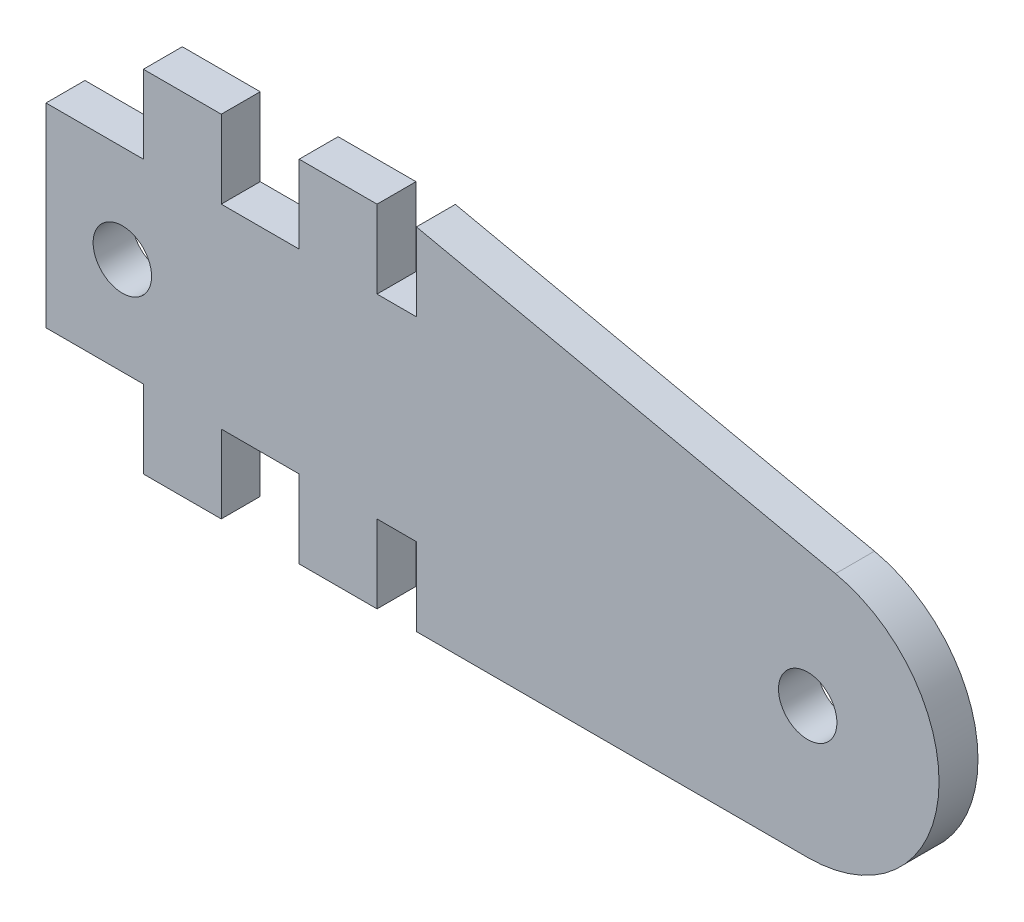
SolidWorks part; units mm, degrees
ref_plane "Front Plane" through (0, 0, 0) normal (0, 0, 1) x (1, 0, 0)
ref_plane "Top Plane" through (0, 0, 0) normal (0, 1, 0) x (1, 0, 0)
ref_plane "Right Plane" through (0, 0, 0) normal (1, 0, 0) x (0, 0, -1)
sketch "Sketch1" plane through (0, 0, 0) normal (0, 0, 1) x (1, 0, 0)
  line L0 (5, 0) -> (9, 0)
  line L1 (5, 4) -> (5, 0)
  line L2 (5, 14) -> (0, 14)
  line L3 (9, 4) -> (13, 4)
  line L4 (13, 4) -> (13, 0)
  line L5 (9, 0) -> (9, 4)
  line L6 (13, 0) -> (17, 0)
  line L7 (17, 0) -> (17, 4)
  line L8 (17, 4) -> (19.0216, 4)
  line L9 (0, 14) -> (0, 4)
  line L10 (19.0216, 4) -> (19.0216, 0)
  line L11 (17, 14) -> (19.0216, 14)
  line L12 (17, 18) -> (17, 14)
  line L13 (13, 18) -> (17, 18)
  line L14 (9, 18) -> (9, 14)
  line L15 (13, 14) -> (13, 18)
  line L16 (9, 14) -> (13, 14)
  line L17 (0, 4) -> (5, 4)
  line L18 (5, 14) -> (5, 18)
  line L19 (5, 18) -> (9, 18)
  line L20 (19.0216, 0) -> (39.1145, 0)
  line L21 (29.045, 0) -> (29.045, -6.4753) construction
  line L22 (19.0216, 14) -> (19.0216, 18)
  line L23 (19.0216, 18) -> (40.5426, 13.3378)
  line L27 (23.6391, 12.0249) -> (21.6695, 11.6776) construction
  line L32 (16.7455, 10.8093) -> (17.6137, 5.8853) construction
  line L33 (16.7455, 10.8093) -> (14.7759, 10.462) construction
  line L34 (14.7759, 10.462) -> (15.6441, 5.538) construction
  line L35 (15.6441, 5.538) -> (17.6137, 5.8853) construction
  line L36 (21.6695, 11.6776) -> (22.5378, 6.7535) construction
  line L37 (22.5378, 6.7535) -> (24.5074, 7.1008) construction
  line L38 (23.6391, 12.0249) -> (24.5074, 7.1008) construction
  arc A0 (39.1145, 0) -> (40.5426, 13.3378) centre (39.1145, 6.7453) ccw
  circle A1 centre (3.9205, 9) radius 1.5
  circle A2 centre (39.1145, 6.7453) radius 12.12 construction
  circle A4 centre (39.1145, 6.7453) radius 1.5
  dimension "D16" = 9
  dimension "D13" = 5.8853
  dimension "D1" = 3
  dimension "D2" = 6.7453
  dimension "D7" = 24.24
  dimension "D3" = 3.9205
  dimension "D4" = 14.7759
  dimension "D5" = 15.6441
  dimension "D6" = 16.7455
  dimension "D8" = 21.6695
  dimension "D9" = 9
  dimension "D10" = 18
  dimension "D11" = 19.0216
  dimension "D12" = 5.538
  dimension "ThumbLinkLengthMCP" = 20.045
extrude "Boss-Extrude1" add sketch "Sketch1" along normal blind 2
equation "\"ThumbLinkLengthMCP@Sketch1\"= \"HB@parametersSketch@prostheticParameters.SLDPRT\" * 0.211"
